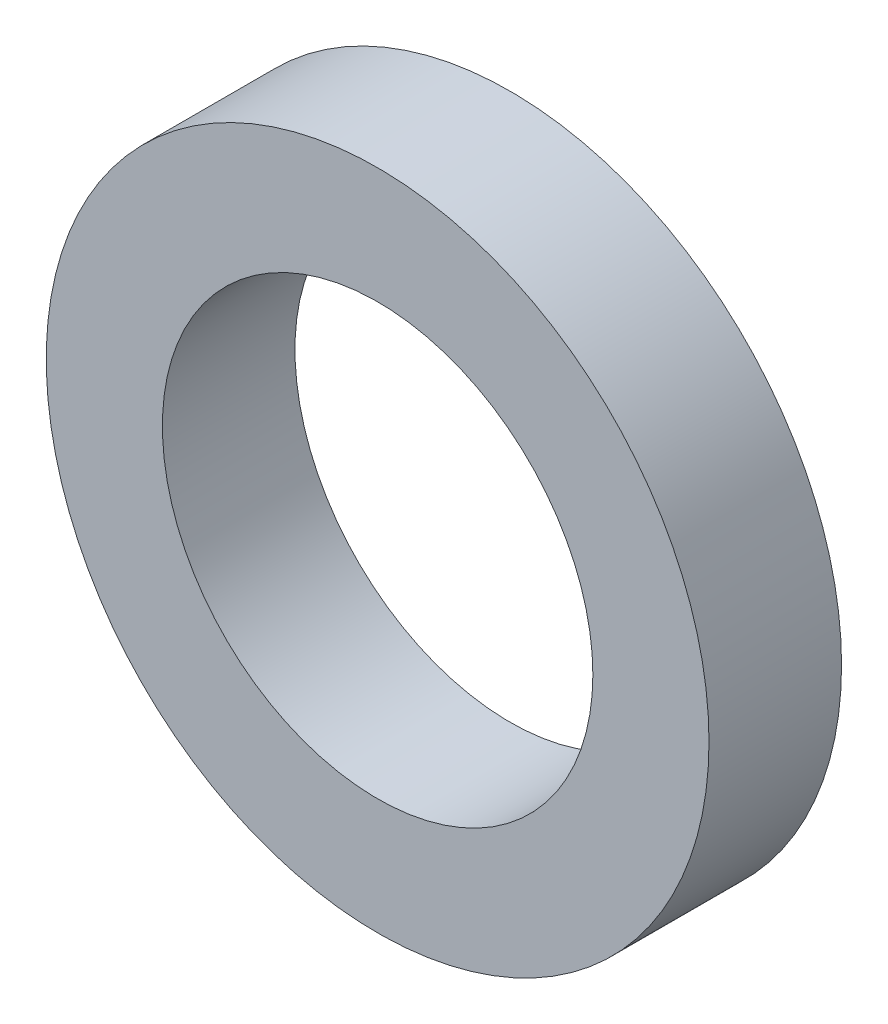
SolidWorks part; units mm, degrees
ref_plane "Front Plane" through (0, 0, 0) normal (0, 0, 1) x (1, 0, 0)
ref_plane "Top Plane" through (0, 0, 0) normal (0, 1, 0) x (1, 0, 0)
ref_plane "Right Plane" through (0, 0, 0) normal (1, 0, 0) x (0, 0, -1)
sketch "Sketch1" plane through (0, 0, 0) normal (0, 0, 1) x (1, 0, 0)
  line L1 (3.75, 0) -> (1.875, 3.2476) construction
  line L2 (1.875, 3.2476) -> (-1.875, 3.2476) construction
  line L3 (-1.875, 3.2476) -> (-3.75, 0) construction
  line L4 (-3.75, 0) -> (-1.875, -3.2476) construction
  line L5 (-1.875, -3.2476) -> (1.875, -3.2476) construction
  line L6 (1.875, -3.2476) -> (3.75, 0) construction
  circle A0 centre (0, 0) radius 3.75 construction
  circle A1 centre (0, 0) radius 3.2476
  circle A2 centre (0, 0) radius 5
  dimension "D1" = 7.5
  dimension "D2" = 10
extrude "Boss-Extrude1" add sketch "Sketch1" along normal blind 2
